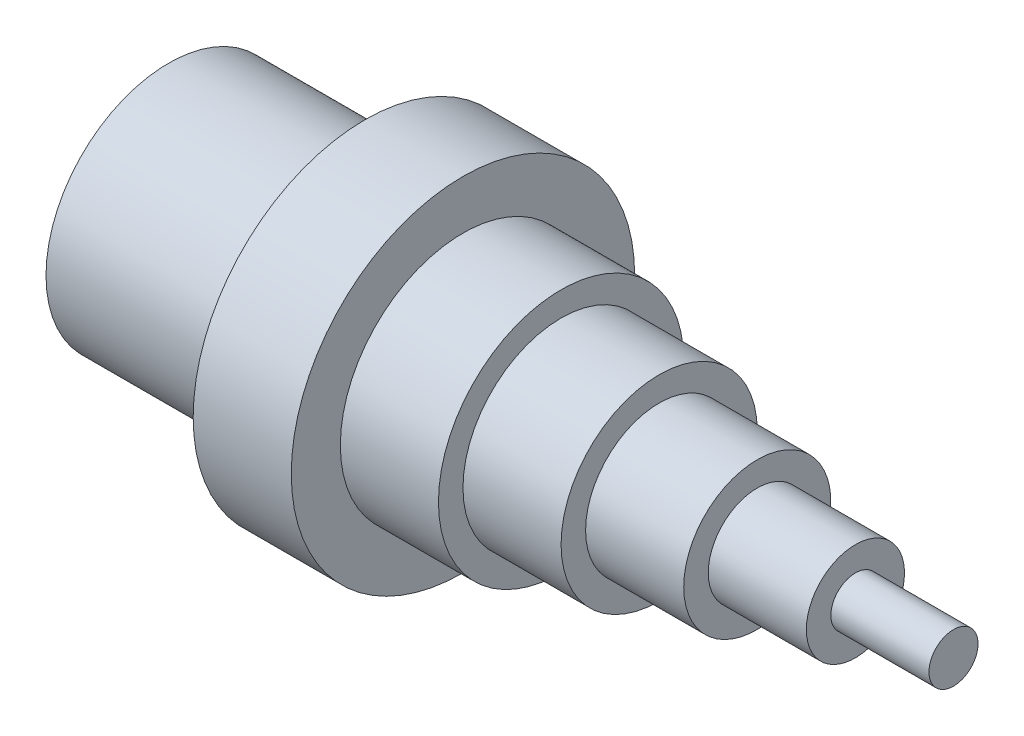
SolidWorks part; units mm, degrees
ref_plane "Front Plane" through (0, 0, 0) normal (0, 0, 1) x (1, 0, 0)
ref_plane "Top Plane" through (0, 0, 0) normal (0, 1, 0) x (1, 0, 0)
ref_plane "Right Plane" through (0, 0, 0) normal (1, 0, 0) x (0, 0, -1)
sketch "Sketch1" plane through (0, 0, 0) normal (0, 0, 1) x (1, 0, 0)
  line L0 (0, 0) -> (232.5775, 0) construction
  line L1 (0, 0) -> (0, 25)
  line L2 (0, 25) -> (40, 25)
  line L3 (40, 25) -> (40, 35)
  line L4 (40, 35) -> (60, 35)
  line L5 (60, 35) -> (60, 25)
  line L6 (60, 25) -> (80, 25)
  line L7 (80, 25) -> (80, 20)
  line L8 (80, 20) -> (100, 20)
  line L9 (100, 20) -> (100, 15)
  line L10 (100, 15) -> (120, 15)
  line L11 (120, 15) -> (120, 10)
  line L12 (120, 10) -> (140, 10)
  line L13 (140, 10) -> (140, 5)
  line L14 (140, 5) -> (160, 5)
  line L15 (160, 5) -> (160, 0)
  line L16 (0, 0) -> (160, 0)
  dimension "D1" = 25
  dimension "D2" = 10
  dimension "D3" = 40
  dimension "D4" = 20
  dimension "D5" = 20
  dimension "D6" = 20
  dimension "D7" = 20
  dimension "D8" = 20
  dimension "D9" = 20
  dimension "D10" = 5
  dimension "D11" = 5
  dimension "D12" = 5
  dimension "D13" = 5
  dimension "D14" = 5
  dimension "D15" = 10
revolve "Revolve2" add sketch "Sketch1" angle 360 about L0
sketch "Sketch2" plane through (0, 0, 0) normal (-1, 0, 0) x (0, 0, 1)
  circle A0 centre (0, 0) radius 20
  dimension "D1" = 20
extrude "Cut-Extrude1" cut sketch "Sketch2" against normal blind 40
